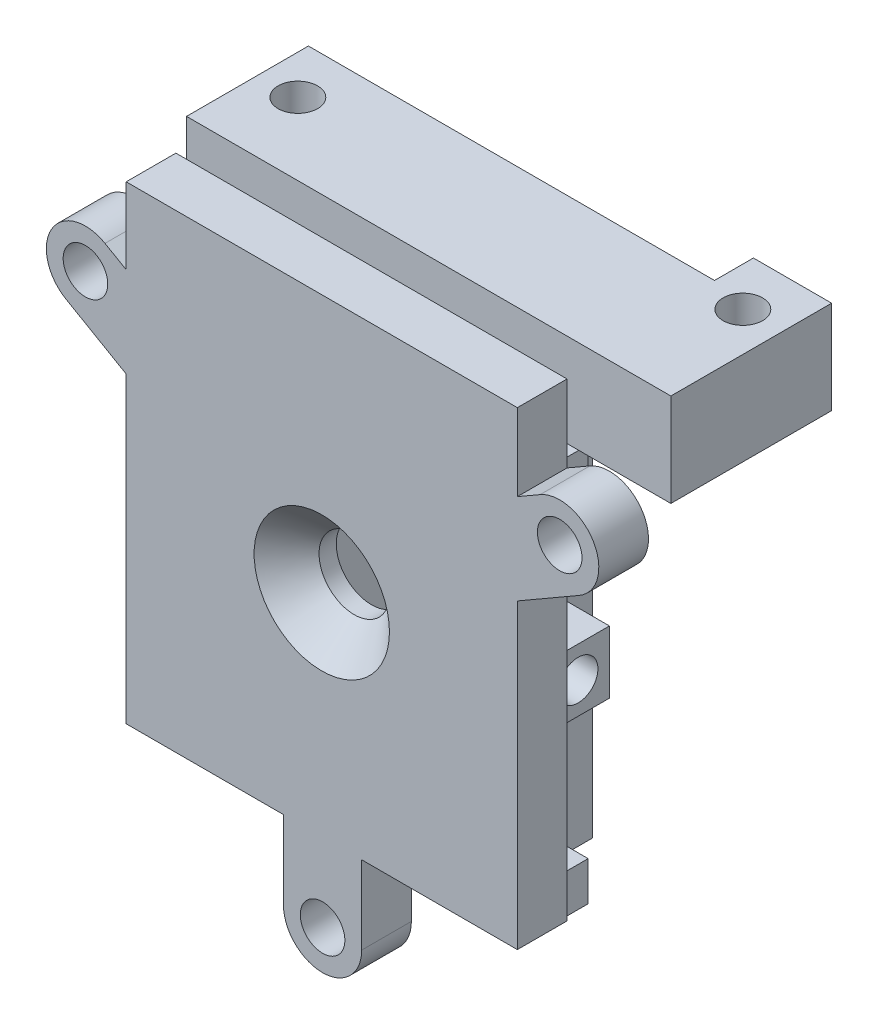
SolidWorks part; units mm, degrees
ref_plane "Front Plane" through (0, 0, 0) normal (0, 0, 1) x (1, 0, 0)
ref_plane "Top Plane" through (0, 0, 0) normal (0, 1, 0) x (1, 0, 0)
ref_plane "Right Plane" through (0, 0, 0) normal (1, 0, 0) x (0, 0, -1)
sketch "Sketch1" plane through (0, 0, 0) normal (0, 0, 1) x (1, 0, 0)
  line L5 (-5, 30) -> (5, 30)
  line L6 (-25, 30) -> (-5, 30)
  line L13 (-25, -30) -> (-4.8977, -30)
  line L31 (5.1023, -30) -> (25, -30)
  line L37 (-4.8977, -30) -> (-4.8977, -40)
  line L39 (5.1023, -30) -> (5.1023, -40)
  line L40 (0.1023, 0) -> (0.1023, -12.7655) construction
  line L41 (0.1023, 0) -> (-30.2086, 17.5) construction
  line L42 (0.1023, 0) -> (30.4132, 17.5) construction
  line L45 (5, 30) -> (25, 30)
  line L61 (25, 30) -> (25, 20.1482)
  line L62 (-25, 30) -> (-25, 20.2663)
  line L63 (-25, 8.7193) -> (-25, -30)
  line L65 (-27.7086, 21.8301) -> (-25, 20.2663)
  line L66 (-32.7086, 13.1699) -> (-25, 8.7193)
  line L67 (27.9132, 21.8301) -> (25, 20.1482)
  line L68 (32.9132, 13.1699) -> (25, 8.6012)
  line L69 (25, 8.6012) -> (25, -30)
  arc A20 (-4.8977, -40) -> (5.1023, -40) centre (0.1023, -40) ccw
  circle A21 centre (0.1023, -40) radius 2.85
  circle A22 centre (30.4132, 17.5) radius 2.85
  circle A23 centre (-30.2086, 17.5) radius 2.85
  arc A29 (-27.7086, 21.8301) -> (-32.7086, 13.1699) centre (-30.2086, 17.5) ccw
  arc A30 (32.9132, 13.1699) -> (27.9132, 21.8301) centre (30.4132, 17.5) ccw
  dimension "D1" = 50
  dimension "D2" = 60
  dimension "D3" = 25
  dimension "D7" = 30
  dimension "D5" = 10
  dimension "D6" = 10
  dimension "D9" = 5
  dimension "D10" = 5.7
  dimension "D11" = 120
  dimension "D12" = 120
  dimension "D13" = 25.1023
  dimension "D15" = 30.3109
  dimension "D14" = 10
  dimension "D17" = 10
  dimension "D16" = 8.9012
  dimension "D4" = 10
  dimension "D8" = 5
  dimension "D18" = 26.4769
  dimension "D19" = 32.1827
  dimension "D20" = 2.7086
  dimension "D21" = 26.4382
  dimension "D22" = 7.9132
  dimension "D23" = 32.1084
  dimension "D24" = 2.9132
extrude "Boss-Extrude1" add sketch "Sketch1" along normal blind 6.35
sketch "Sketch2" plane through (0, 0, 0) normal (0, 0, -1) x (-1, 0, 0)
  line L0 (-12.7, 34.75) -> (12.7, 34.75)
  line L2 (-12.7, 34.75) -> (-12.7, -34.75)
  line L3 (-12.7, -34.75) -> (12.7, -34.75)
  line L4 (12.7, 34.75) -> (12.7, -34.75)
  line L5 (-7.35, 23.4) -> (7.35, 23.4)
  line L6 (-7.35, 23.4) -> (-7.35, -29.4)
  line L7 (-7.35, -29.4) -> (7.35, -29.4)
  line L8 (7.35, 23.4) -> (7.35, -29.4)
  point P8 (-12.7, 0)
  point P13 (0, -34.75)
  dimension "D3" = 14.7
  dimension "D1" = 69.5
  dimension "D2" = 25.4
  dimension "D4" = 5.35
  dimension "D5" = 5.35
  dimension "D6" = 52.8
extrude "Boss-Extrude2" add sketch "Sketch2" along normal blind 15.5784
hole_wizard "CSK for M8 Flat Head Machine Screw1" positions "Sketch3" profile "Sketch4" countersink size "M8" standard "ANSI Metric"
sketch "Sketch3" plane through (0, 0, 6.35) normal (0, 0, 1) x (1, 0, 0)
  point P5 (0, -3)
  dimension "D1" = 3
sketch "Sketch4" plane through (0, -3, 6.35) normal (1, 0, 0) x (0, -1, 0)
  line L0 (0, 0) -> (0, 20.2039)
  line L1 (0, 20.2039) -> (4.5, 17.5)
  line L2 (4.5, 17.5) -> (4.5, 4.15)
  line L3 (4.5, 4.15) -> (8.65, 0)
  line L5 (8.65, 0) -> (0, 0)
  line L6 (-4.5, 4.15) -> (-8.65, 0) construction
  line L10 (0, 20.2039) -> (-4.5, 17.5) construction
  line L11 (0, -6.35) -> (0, 107.95) construction
  dimension "Hole Dia." = 9
  dimension "Hole Depth" = 17.5
  dimension "Near C'Sink Dia." = 17.3
  dimension "Near C'Sink Angle" = 90
  dimension "Drill Angle" = 118
sketch "Sketch6" plane through (12.7, 0, 0) normal (1, 0, 0) x (0, 0, -1)
  line L0 (15.5784, 34.75) -> (15.5784, -34.75) construction
  line L1 (0, 34.75) -> (15.5784, 34.75)
  line L2 (0, 34.75) -> (0, 22.85)
  line L3 (0, 22.85) -> (15.5784, 22.85)
  line L4 (15.5784, 34.75) -> (15.5784, 22.85)
  dimension "D1" = 11.9
extrude "Boss-Extrude3" add sketch "Sketch6" along normal blind 25.5721
sketch "Sketch7" plane through (-12.7, 0, 0) normal (-1, 0, 0) x (0, 0, 1)
  line L1 (-15.5784, 34.75) -> (0, 34.75)
  line L2 (-15.5784, 34.75) -> (-15.5784, 22.85)
  line L3 (-15.5784, 22.85) -> (0, 22.85)
  line L4 (0, 34.75) -> (0, 22.85)
  dimension "D1" = 11.9
extrude "Boss-Extrude4" add sketch "Sketch7" along normal blind 10.9373
sketch "Sketch8" plane through (0, 34.75, 0) normal (0, 1, 0) x (1, 0, 0)
  line L1 (-23.6373, 0) -> (-23.6373, 15.5784) construction
  line L3 (-23.6373, 15.5784) -> (38.2721, 15.5784) construction
  circle A0 centre (-18.6373, 9.2284) radius 2.5273
  dimension "D1" = 5.0546
  dimension "D2" = 6.35
  dimension "D3" = 5
extrude "Cut-Extrude1" cut sketch "Sketch8" against normal blind 7
sketch "Sketch9" plane through (0, 0, -15.5784) normal (0, 0, -1) x (-1, 0, 0)
  line L1 (-38.2721, 34.75) -> (-28.2721, 34.75)
  line L2 (-38.2721, 34.75) -> (-38.2721, 22.85)
  line L3 (-38.2721, 22.85) -> (-28.2721, 22.85)
  line L4 (-28.2721, 34.75) -> (-28.2721, 22.85)
  dimension "D1" = 10
extrude "Boss-Extrude5" add sketch "Sketch9" along normal blind 4.9727
sketch "Sketch10" plane through (0, 34.75, 0) normal (0, 1, 0) x (1, 0, 0)
  line L0 (38.2721, 20.5511) -> (38.2721, 0) construction
  line L1 (28.2721, 20.5511) -> (38.2721, 20.5511) construction
  circle A0 centre (33.2721, 14.2011) radius 2.5273
  circle A1 centre (-18.6373, 9.2284) radius 2.5273 construction
  dimension "D1" = 5
  dimension "D2" = 6.35
extrude "Cut-Extrude2" cut sketch "Sketch10" against normal blind 7
sketch "Sketch11" plane through (12.7, 0, 0) normal (1, 0, 0) x (0, 0, -1)
  line L0 (15.5784, 22.85) -> (15.5784, -34.75) construction
  line L1 (15.5784, -3.175) -> (20.9169, -3.175)
  line L2 (15.5784, -3.175) -> (15.5784, -13.175)
  line L3 (15.5784, -13.175) -> (20.9169, -13.175)
  line L4 (20.9169, -3.175) -> (20.9169, -13.175)
  line L5 (0, 22.85) -> (20.5511, 22.85) construction
  dimension "D1" = 26.025
  dimension "D2" = 10
  dimension "D3" = 5.3384
extrude "Boss-Extrude6" add sketch "Sketch11" against normal up to surface (5.35 mm away) up to face at (7.35, -3, -7.7892)
sketch "Sketch14" plane through (0, 0, -20.9169) normal (0, 0, -1) x (-1, 0, 0)
  line L6 (-12.7, -3.175) -> (-7.35, -3.175)
  line L7 (-12.7, -3.175) -> (-12.7, -13.175)
  line L8 (-12.7, -13.175) -> (-7.35, -13.175)
  line L9 (-7.35, -3.175) -> (-7.35, -13.175)
extrude "Cut-Extrude4" cut sketch "Sketch14" against normal up to surface (5.3384 mm away) up to face at (3.0856, 2.9188, -15.5784)
sketch "Sketch15" plane through (12.7, 0, 0) normal (1, 0, 0) x (0, 0, -1)
  line L0 (0, 8.6012) -> (0, 13.1699) construction
  line L1 (2, 17.05) -> (7, 17.05)
  line L2 (2, 17.05) -> (2, 12.05)
  line L3 (2, 12.05) -> (7, 12.05)
  line L4 (7, 17.05) -> (7, 12.05)
  line L5 (15.5784, -34.75) -> (0, -34.75) construction
  line L6 (2, -28.75) -> (7, -28.75)
  line L7 (2, -28.75) -> (2, -33.75)
  line L8 (2, -33.75) -> (7, -33.75)
  line L9 (7, -28.75) -> (7, -33.75)
  line L11 (1.72, -4.35) -> (9.72, -4.35)
  line L12 (1.72, -4.35) -> (1.72, -12.35)
  line L13 (1.72, -12.35) -> (9.72, -12.35)
  line L14 (9.72, -4.35) -> (9.72, -12.35)
  point P10 (4.5, -33.75)
  point P17 (5.72, -4.35)
  point P18 (9.72, -8.35)
  dimension "D1" = 2
  dimension "D2" = 5
  dimension "D3" = 5
  dimension "D4" = 50.8
  dimension "D5" = 1
  dimension "D6" = 8
  dimension "D7" = 8
  dimension "D8" = 3.72
  dimension "D9" = 25.4
extrude "Boss-Extrude7" add sketch "Sketch15" along normal blind 8
sketch "Sketch16" plane through (20.7, 0, 0) normal (1, 0, 0) x (0, 0, -1)
  line L0 (1.72, -12.35) -> (9.72, -12.35) construction
  line L1 (9.72, -12.35) -> (9.72, -4.35) construction
  circle A0 centre (5.72, -8.35) radius 2.5273
  point P2 (0, 0)
  point P5 (5.72, -12.35)
  point P8 (9.72, -8.35)
  dimension "D1" = 5.0546
extrude "Cut-Extrude5" cut sketch "Sketch16" against normal blind 7
